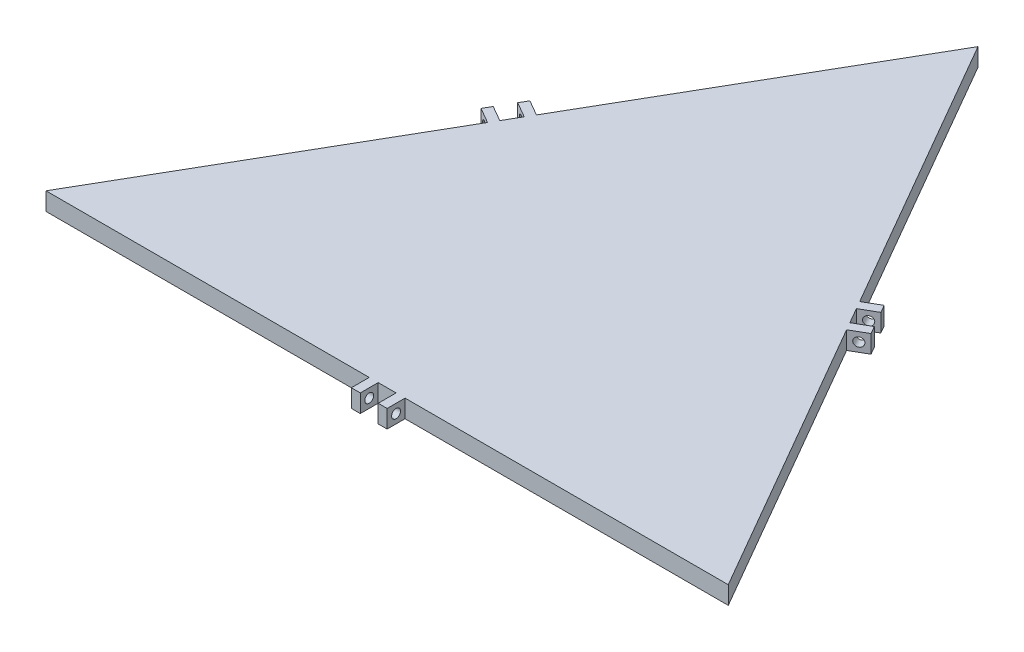
SolidWorks part; units mm, degrees
ref_plane "Front Plane" through (0, 0, 0) normal (0, 0, 1) x (1, 0, 0)
ref_plane "Top Plane" through (0, 0, 0) normal (0, 1, 0) x (1, 0, 0)
ref_plane "Right Plane" through (0, 0, 0) normal (1, 0, 0) x (0, 0, -1)
sketch "Sketch1" plane through (0, 0, 0) normal (0, 1, 0) x (1, 0, 0)
  line L0 (-381.1, 0) -> (-190.55, 330.0423)
  line L1 (-190.55, 330.0423) -> (0, 0)
  line L2 (0, 0) -> (-381.1, 0)
  dimension "D1" = 381.1
extrude "Boss-Extrude1" add sketch "Sketch1" along normal blind 10
sketch "Sketch2" plane through (0, 0, 0) normal (0.866, 0, -0.5) x (-0.5, 0, -0.866)
  line L0 (0, 10) -> (0, 0) construction
  line L4 (190.55, 10) -> (190.55, 0) construction
  line L5 (381.1, 10) -> (381.1, 0) construction
  dimension "D1" = 190.55
other "AlignGroup1" parameters "D1"=90, "D2"=190.55
sketch "Sketch3" plane through (0, 0, 0) normal (0.866, 0, -0.5) x (-0.5, 0, -0.866)
  line L0 (0, 10) -> (381.1, 10) construction
  line L1 (195.55, 10) -> (200.55, 10)
  line L2 (195.55, 10) -> (195.55, 0)
  line L3 (195.55, 0) -> (200.55, 0)
  line L4 (200.55, 10) -> (200.55, 0)
  line L5 (0, 0) -> (381.1, 0) construction
  line L6 (190.55, 10) -> (190.55, 0) construction
  line L7 (185.55, 10) -> (180.55, 10)
  line L8 (185.55, 10) -> (185.55, 0)
  line L9 (185.55, 0) -> (180.55, 0)
  line L10 (180.55, 10) -> (180.55, 0)
  dimension "D1" = 5
  dimension "D2" = 5
  dimension "D3" = 5
extrude "Boss-Extrude2" add sketch "Sketch3" along normal blind 10
ref_plane "Plane1" through (-190.55, 0, 0) normal (1, 0, 0) x (0, 0, -1)
ref_plane "Plane2" through (0, 0, 0) normal (-0.5, 0, 0.866) x (0.866, 0, 0.5)
sketch "Sketch5" plane through (-90.275, 0, -156.3609) normal (0.5, 0, 0.866) x (0.866, 0, -0.5)
  line L0 (10, 10) -> (0, 10) construction
  line L1 (10, 10) -> (10, 0) construction
  circle A0 centre (5, 5) radius 2.5
  point P4 (5, 10)
  point P7 (10, 5)
  dimension "D1" = 5
extrude "Cut-Extrude1" cut sketch "Sketch5" along direction (0.5, 0, 0.866) on the side against the normal blind 20
mirror "Mirror1" about plane through (0, 0, 0) normal (-0.5, 0, 0.866) of "Boss-Extrude2", "Cut-Extrude1"
mirror "Mirror2" about plane through (-190.55, 0, 0) normal (1, 0, 0) of "Mirror1", "Boss-Extrude2", "Cut-Extrude1"
equation "\"D2@Sketch3\"=\"D1@Sketch3\""
